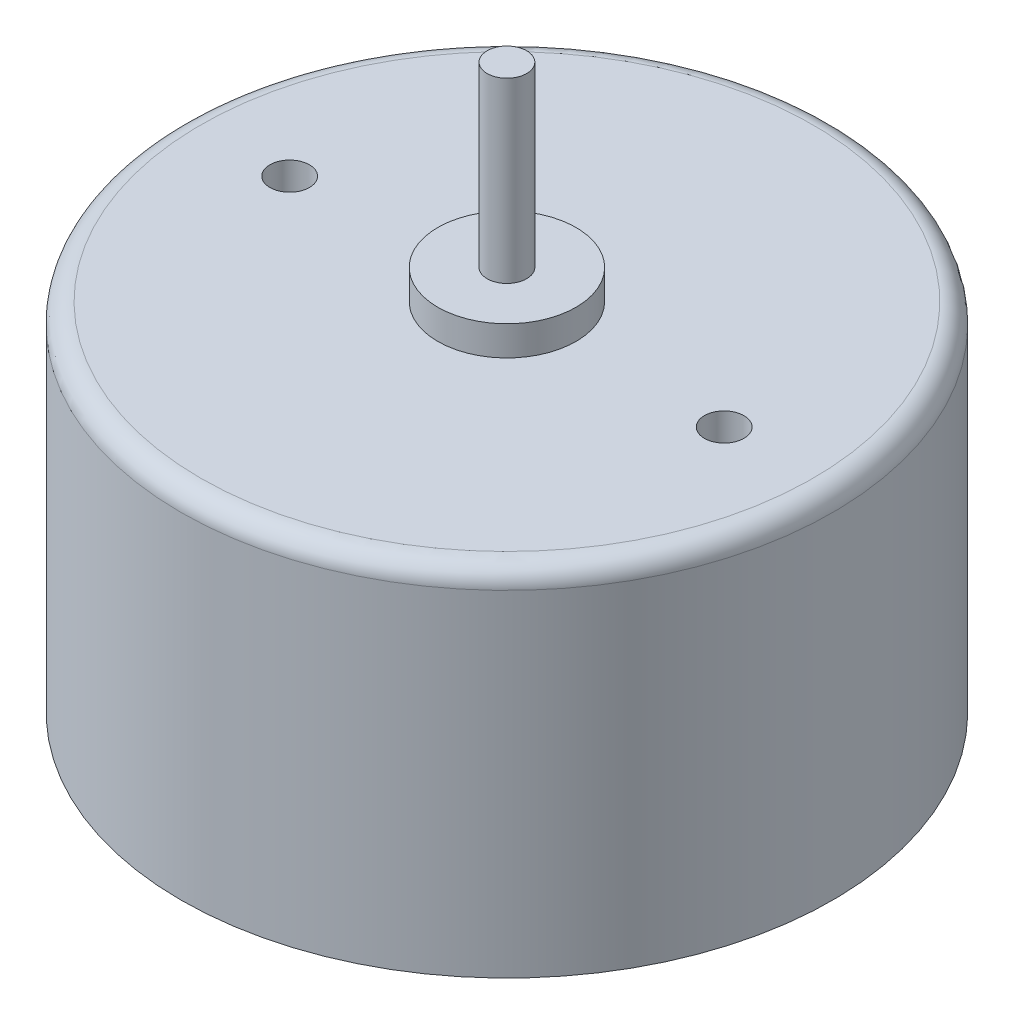
SolidWorks part; units mm, degrees
material "1060 Alloy"
ref_plane "Front Plane" through (0, 0, 0) normal (0, 0, 1) x (1, 0, 0)
ref_plane "Top Plane" through (0, 0, 0) normal (0, 1, 0) x (1, 0, 0)
ref_plane "Right Plane" through (0, 0, 0) normal (1, 0, 0) x (0, 0, -1)
sketch "Sketch1" plane through (0, 0, 0) normal (0, 1, 0) x (1, 0, 0)
  circle A0 centre (0, 0) radius 16.5
  dimension "D1" = 33
extrude "Boss-Extrude1" add sketch "Sketch1" along normal blind 18
sketch "Sketch2" plane through (0, 18, 0) normal (0, 1, 0) x (1, 0, 0)
  circle A0 centre (0, 0) radius 3.5
  dimension "D1" = 7
extrude "Boss-Extrude2" add sketch "Sketch2" along normal blind 1.5
sketch "Sketch3" plane through (0, 19.5, 0) normal (0, 1, 0) x (1, 0, 0)
  circle A0 centre (0, 0) radius 1
  dimension "D1" = 2
extrude "Boss-Extrude3" add sketch "Sketch3" along normal blind 9
fillet "Fillet1" radius 1 1 edges at (0, 18, 16.5)
sketch "Sketch4" plane through (0, 18, 0) normal (0, 1, 0) x (1, 0, 0)
  circle A0 centre (11, 0) radius 1
  circle A1 centre (-11, 0) radius 1
  point P7 (0, 0)
  dimension "D1" = 2
  dimension "D2" = 11
  dimension "D3" = 2
extrude "Cut-Extrude1" cut sketch "Sketch4" against normal blind 1.5
sketch "Sketch5" plane through (0, 0, 0) normal (0, -1, 0) x (1, 0, 0)
  circle A0 centre (0, 0) radius 3.5
  dimension "D1" = 7
extrude "Boss-Extrude4" add sketch "Sketch5" along normal blind 3
sketch "Sketch6" plane through (0, 0, 0) normal (0, -1, 0) x (1, 0, 0)
  circle A2 centre (0, 0) radius 15.8
  circle A3 centre (0, 0) radius 15.8
  circle A5 centre (0, 0) radius 3.5
  circle A6 centre (0, 0) radius 3.5
  dimension "D1" = 0.7
  dimension "D2" = 0
extrude "Cut-Extrude2" cut sketch "Sketch6" against normal blind 0.5
